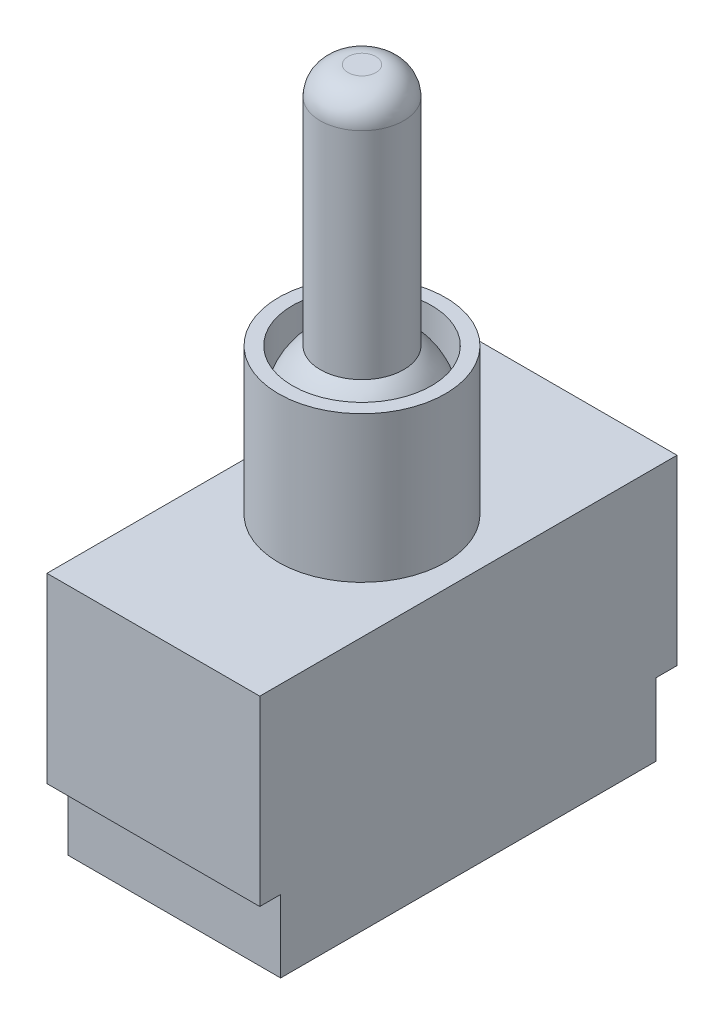
SolidWorks part; units mm, degrees
ref_plane "Спереди" through (0, 0, 0) normal (0, 0, 1) x (1, 0, 0)
ref_plane "Сверху" through (0, 0, 0) normal (0, 1, 0) x (1, 0, 0)
ref_plane "Справа" through (0, 0, 0) normal (1, 0, 0) x (0, 0, -1)
sketch "Sketch1" plane through (0, 0, 0) normal (0, 1, 0) x (1, 0, 0)
  line L1 (7.65, -15) -> (-7.65, -15)
  line L2 (7.65, -15) -> (7.65, 15)
  line L3 (7.65, 15) -> (-7.65, 15)
  line L4 (-7.65, -15) -> (-7.65, 15)
  line L5 (7.65, -15) -> (-7.65, 15) construction
  line L6 (7.65, 15) -> (-7.65, -15) construction
  point P0 (0, 0)
  dimension "D1" = 15.3
  dimension "D2" = 30
extrude "Boss-Extrude1" add sketch "Sketch1" along normal blind 13.1
sketch "Sketch2" plane through (0, 13.1, 0) normal (0, 1, 0) x (1, 0, 0)
  line L0 (-7.65, 15) -> (7.65, -15) construction
  circle A0 centre (0, 0) radius 6
  dimension "D1" = 12
extrude "Boss-Extrude2" add sketch "Sketch2" along normal blind 10.5
sketch "Sketch4" plane through (0, 23.6, 0) normal (0, 1, 0) x (1, 0, 0)
  circle A0 centre (0, 0) radius 5
  dimension "D1" = 10
extrude "Cut-Extrude1" cut sketch "Sketch4" against normal blind 4
sketch "Sketch5" plane through (0, 19.6, 0) normal (0, 1, 0) x (1, 0, 0)
  circle A0 centre (0, 0) radius 3
  dimension "D1" = 6
extrude "Boss-Extrude3" add sketch "Sketch5" along normal blind 21.5
sketch "Sketch3" plane through (0, 19.6, 0) normal (0, 1, 0) x (1, 0, 0)
  line L0 (0, -6) -> (0, 6) construction
  line L1 (0, -5) -> (0, 5)
  circle A0 centre (0, 0) radius 6 construction
  arc A1 (0, -5) -> (0, 5) centre (0, 0) cw
  point P7 (0, 0)
  dimension "D1" = 10
revolve "Revolve2" add sketch "Sketch3" angle 180 about L0
fillet "Fillet1" radius 2 1 edges at (0, 41.1, 3)
sketch "Sketch6" plane through (0, 0, 0) normal (0, -1, 0) x (1, 0, 0)
  line L0 (-7.65, -15) -> (-7.65, 15) construction
  line L1 (7.65, 13.5) -> (-7.65, 13.5)
  line L2 (7.65, 13.5) -> (7.65, -13.5)
  line L3 (7.65, -13.5) -> (-7.65, -13.5)
  line L4 (-7.65, 13.5) -> (-7.65, -13.5)
  line L5 (7.65, 13.5) -> (-7.65, -13.5) construction
  line L6 (7.65, -13.5) -> (-7.65, 13.5) construction
  point P0 (0, 0)
  dimension "D1" = 27
extrude "Boss-Extrude4" add sketch "Sketch6" along normal blind 5.2
